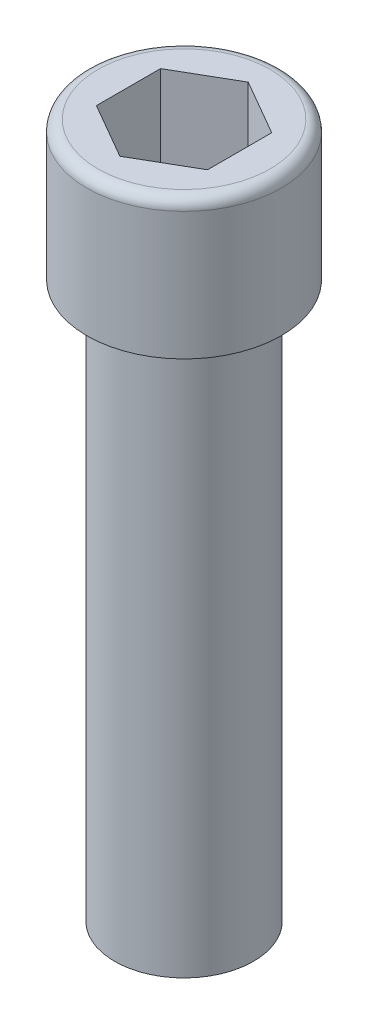
SolidWorks part; units mm, degrees
ref_plane "Front Plane" through (0, 0, 0) normal (0, 0, 1) x (1, 0, 0)
ref_plane "Top Plane" through (0, 0, 0) normal (0, 1, 0) x (1, 0, 0)
ref_plane "Right Plane" through (0, 0, 0) normal (1, 0, 0) x (0, 0, -1)
sketch "Sketch1" plane through (0, 0, 0) normal (0, 1, 0) x (1, 0, 0)
  circle A0 centre (0, 0) radius 1.75
  dimension "D1" = 3.5
extrude "Boss-Extrude1" add sketch "Sketch1" along normal blind 2.5
sketch "Sketch3" plane through (0, 0, 0) normal (0, -1, 0) x (1, 0, 0)
  circle A0 centre (0, 0) radius 1.25
  dimension "D1" = 2.5
extrude "Boss-Extrude2" add sketch "Sketch3" along normal blind 10
fillet "Fillet1" radius 0.2 1 edges at (0, 2.5, 1.75)
sketch "Sketch4" plane through (0, 2.5, 0) normal (0, 1, 0) x (1, 0, 0)
  line L1 (0, -1.1547) -> (1, -0.5774)
  line L2 (1, -0.5774) -> (1, 0.5774)
  line L3 (1, 0.5774) -> (0, 1.1547)
  line L4 (0, 1.1547) -> (-1, 0.5774)
  line L5 (-1, 0.5774) -> (-1, -0.5774)
  line L6 (-1, -0.5774) -> (0, -1.1547)
  circle A0 centre (0, 0) radius 1 construction
  dimension "D1" = 2
extrude "Cut-Extrude1" cut sketch "Sketch4" against normal blind 1.5
